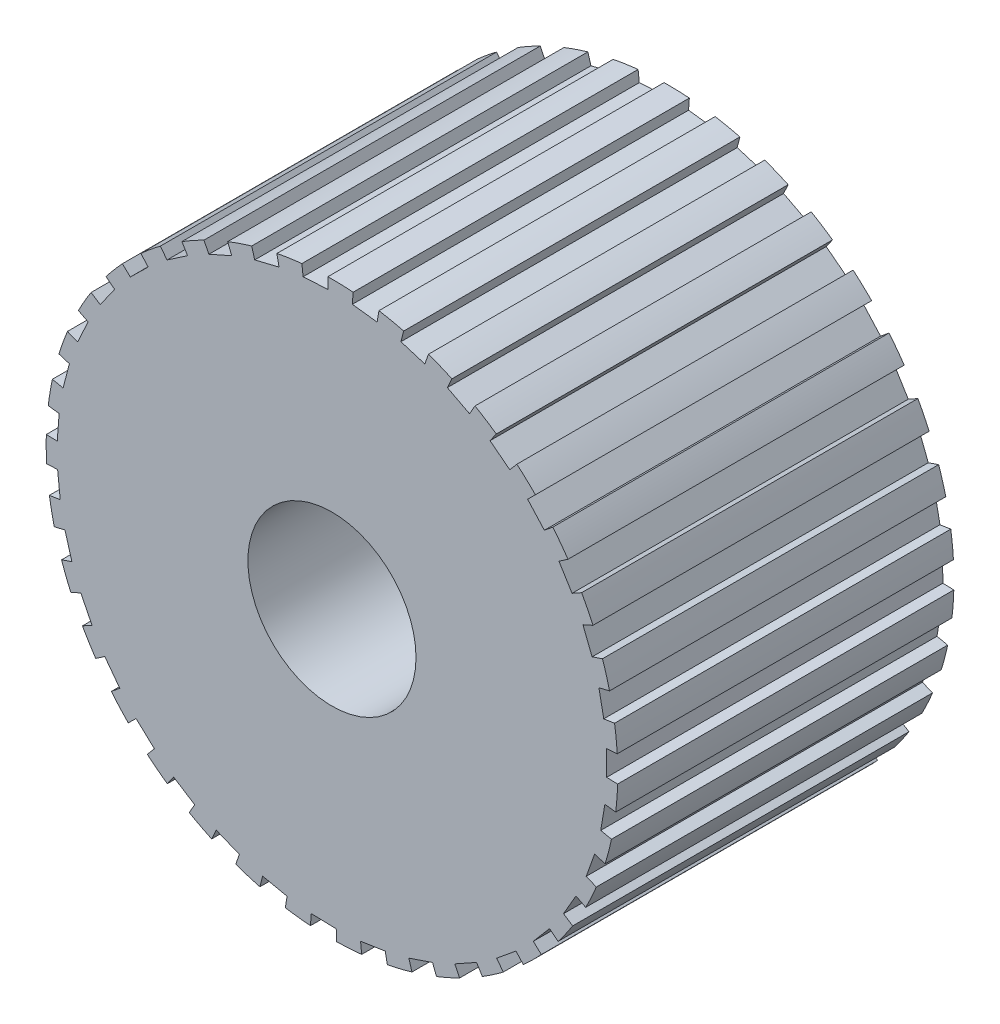
SolidWorks part; units mm, degrees
ref_plane "Front Plane" through (0, 0, 0) normal (0, 0, 1) x (1, 0, 0)
ref_plane "Top Plane" through (0, 0, 0) normal (0, 1, 0) x (1, 0, 0)
ref_plane "Right Plane" through (0, 0, 0) normal (1, 0, 0) x (0, 0, -1)
sketch "Sketch1" plane through (0, 0, 0) normal (0, 0, 1) x (1, 0, 0)
  line L0 (-2.3888, 8.1574) -> (-2.2972, 7.8448)
  line L1 (-2.2972, 7.8448) -> (-1.5752, 8.0211)
  line L2 (-1.5752, 8.0211) -> (-1.638, 8.3407)
  line L3 (-1.9362, 7.933) -> (0, 0) construction
  line L4 (-0.8596, 8.129) -> (-0.1177, 8.1734)
  line L5 (-0.8938, 8.4529) -> (-0.8596, 8.129)
  line L6 (-0.1177, 8.1734) -> (-0.1223, 8.4991)
  line L7 (0.6057, 8.1518) -> (1.3437, 8.0631)
  line L8 (0.6299, 8.4766) -> (0.6057, 8.1518)
  line L9 (1.3437, 8.0631) -> (1.3972, 8.3844)
  line L10 (2.0515, 7.9126) -> (2.7618, 7.6936)
  line L11 (2.1333, 8.2279) -> (2.0515, 7.9126)
  line L12 (2.7618, 7.6936) -> (2.8718, 8.0002)
  line L13 (3.4314, 7.4192) -> (4.0911, 7.0768)
  line L14 (3.5682, 7.7148) -> (3.4314, 7.4192)
  line L15 (4.0911, 7.0768) -> (4.2542, 7.3588)
  line L16 (4.701, 6.6872) -> (5.289, 6.2326)
  line L17 (4.8884, 6.9537) -> (4.701, 6.6872)
  line L18 (5.289, 6.2326) -> (5.4998, 6.4809)
  line L19 (5.8195, 5.7404) -> (6.3169, 5.188)
  line L20 (6.0514, 5.9691) -> (5.8195, 5.7404)
  line L21 (6.3169, 5.188) -> (6.5686, 5.3948)
  line L22 (6.751, 4.609) -> (7.1417, 3.9767)
  line L23 (7.02, 4.7927) -> (6.751, 4.609)
  line L24 (7.1417, 3.9767) -> (7.4263, 4.1352)
  line L25 (7.4655, 3.3295) -> (7.737, 2.6376)
  line L26 (7.763, 3.4622) -> (7.4655, 3.3295)
  line L27 (7.737, 2.6376) -> (8.0453, 2.7427)
  line L28 (7.94, 1.943) -> (8.0837, 1.2137)
  line L29 (8.2564, 2.0204) -> (7.94, 1.943)
  line L30 (8.0837, 1.2137) -> (8.4058, 1.2621)
  line L31 (8.1593, 0.494) -> (8.1705, -0.2492)
  line L32 (8.4845, 0.5137) -> (8.1593, 0.494)
  line L33 (8.1705, -0.2492) -> (8.4961, -0.2591)
  line L34 (8.1164, -0.9708) -> (7.9947, -1.704)
  line L35 (8.4398, -1.0095) -> (8.1164, -0.9708)
  line L36 (7.9947, -1.704) -> (8.3133, -1.772)
  line L37 (7.8126, -2.4045) -> (7.5619, -3.1042)
  line L38 (8.1239, -2.5003) -> (7.8126, -2.4045)
  line L39 (7.5619, -3.1042) -> (7.8633, -3.2279)
  line L40 (7.2577, -3.7608) -> (6.8861, -4.4045)
  line L41 (7.5469, -3.9107) -> (7.2577, -3.7608)
  line L42 (6.8861, -4.4045) -> (7.1605, -4.58)
  line L43 (6.4696, -4.9963) -> (5.989, -5.5633)
  line L44 (6.7274, -5.1954) -> (6.4696, -4.9963)
  line L45 (5.989, -5.5633) -> (6.2277, -5.785)
  line L46 (5.4735, -6.0712) -> (4.8994, -6.5433)
  line L47 (5.6916, -6.3131) -> (5.4735, -6.0712)
  line L48 (4.8994, -6.5433) -> (5.0946, -6.804)
  line L49 (4.3015, -6.951) -> (3.6523, -7.313)
  line L50 (4.4729, -7.228) -> (4.3015, -6.951)
  line L51 (3.6523, -7.313) -> (3.7979, -7.6044)
  line L52 (2.9912, -7.6073) -> (2.2879, -7.8476)
  line L53 (3.1104, -7.9105) -> (2.9912, -7.6073)
  line L54 (2.2879, -7.8476) -> (2.379, -8.1603)
  line L55 (1.5848, -8.0192) -> (0.8498, -8.13)
  line L56 (1.6479, -8.3387) -> (1.5848, -8.0192)
  line L57 (0.8498, -8.13) -> (0.8837, -8.4539)
  line L58 (0.1274, -8.1733) -> (-0.6155, -8.1511)
  line L59 (0.1325, -8.499) -> (0.1274, -8.1733)
  line L60 (-0.6155, -8.1511) -> (-0.64, -8.4759)
  line L61 (-1.334, -8.0647) -> (-2.061, -7.9102)
  line L62 (-1.3872, -8.386) -> (-1.334, -8.0647)
  line L63 (-2.061, -7.9102) -> (-2.1431, -8.2254)
  line L64 (-2.7526, -7.6969) -> (-3.4403, -7.4151)
  line L65 (-2.8623, -8.0036) -> (-2.7526, -7.6969)
  line L66 (-3.4403, -7.4151) -> (-3.5774, -7.7105)
  line L67 (-4.0827, -7.0817) -> (-4.709, -6.6816)
  line L68 (-4.2454, -7.3639) -> (-4.0827, -7.0817)
  line L69 (-4.709, -6.6816) -> (-4.8967, -6.9478)
  line L70 (-5.2815, -6.2389) -> (-5.8264, -5.7334)
  line L71 (-5.492, -6.4875) -> (-5.2815, -6.2389)
  line L72 (-5.8264, -5.7334) -> (-6.0586, -5.9619)
  line L73 (-6.3107, -5.1956) -> (-6.7565, -4.6009)
  line L74 (-6.5621, -5.4026) -> (-6.3107, -5.1956)
  line L75 (-6.7565, -4.6009) -> (-7.0257, -4.7842)
  line L76 (-7.137, -3.9853) -> (-7.4695, -3.3206)
  line L77 (-7.4214, -4.1441) -> (-7.137, -3.9853)
  line L78 (-7.4695, -3.3206) -> (-7.7671, -3.4529)
  line L79 (-7.7339, -2.6469) -> (-7.9423, -1.9335)
  line L80 (-8.042, -2.7524) -> (-7.7339, -2.6469)
  line L81 (-7.9423, -1.9335) -> (-8.2588, -2.0105)
  line L82 (-8.0822, -1.2234) -> (-8.1599, -0.4842)
  line L83 (-8.4043, -1.2722) -> (-8.0822, -1.2234)
  line L84 (-8.1599, -0.4842) -> (-8.4851, -0.5035)
  line L85 (-8.1708, 0.2394) -> (-8.1152, 0.9806)
  line L86 (-8.4964, 0.2489) -> (-8.1708, 0.2394)
  line L87 (-8.1152, 0.9806) -> (-8.4386, 1.0196)
  line L88 (-7.9967, 1.6945) -> (-7.8098, 2.4138)
  line L89 (-8.3154, 1.762) -> (-7.9967, 1.6945)
  line L90 (-7.8098, 2.4138) -> (-8.121, 2.51)
  line L91 (-7.5656, 3.0951) -> (-7.2532, 3.7695)
  line L92 (-7.8671, 3.2185) -> (-7.5656, 3.0951)
  line L93 (-7.2532, 3.7695) -> (-7.5423, 3.9197)
  line L94 (-6.8914, 4.3963) -> (-6.4636, 5.0041)
  line L95 (-7.166, 4.5715) -> (-6.8914, 4.3963)
  line L96 (-6.4636, 5.0041) -> (-6.7212, 5.2035)
  line L97 (-5.9957, 5.5561) -> (-5.4662, 6.0778)
  line L98 (-6.2346, 5.7775) -> (-5.9957, 5.5561)
  line L99 (-5.4662, 6.0778) -> (-5.684, 6.3199)
  line L100 (-4.9072, 6.5374) -> (-4.2931, 6.9561)
  line L101 (-5.1028, 6.7979) -> (-4.9072, 6.5374)
  line L102 (-4.2931, 6.9561) -> (-4.4642, 7.2333)
  line L103 (-3.6611, 7.3086) -> (-2.9821, 7.6109)
  line L104 (-3.807, 7.5998) -> (-3.6611, 7.3086)
  line L105 (-2.9821, 7.6109) -> (-3.1009, 7.9142)
  circle A0 centre (0, 0) radius 8.5
  point P146 (0, 0)
  dimension "D1" = 17
  dimension "D2" = 35
extrude "Boss-Extrude1" add sketch "Sketch1" along normal blind 10
sketch "Sketch2" plane through (0, 0, 10) normal (0, 0, 1) x (1, 0, 0)
  circle A0 centre (0, 0) radius 2.5
  dimension "D1" = 5
extrude "Cut-Extrude1" cut sketch "Sketch2" against normal through all
